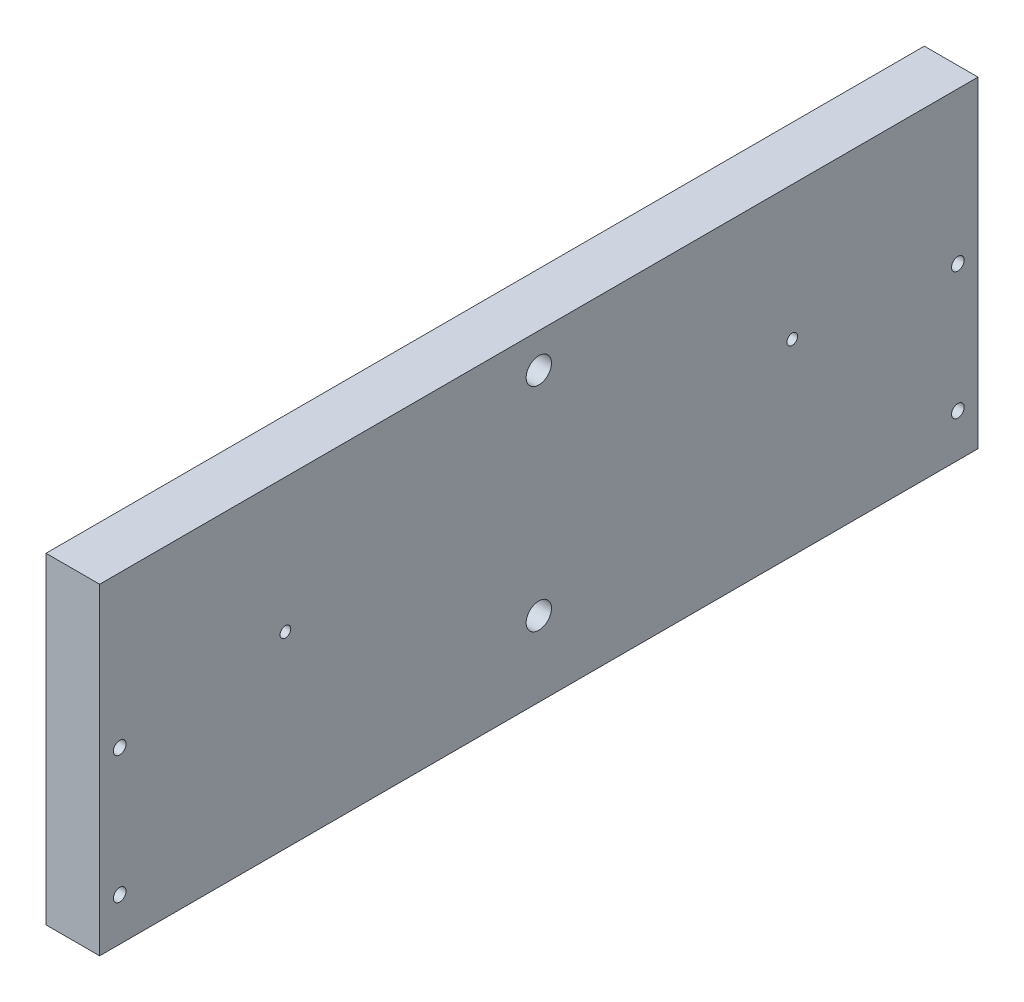
SolidWorks part; units mm, degrees
ref_plane "Front Plane" through (0, 0, 0) normal (0, 0, 1) x (1, 0, 0)
ref_plane "Top Plane" through (0, 0, 0) normal (0, 1, 0) x (1, 0, 0)
ref_plane "Right Plane" through (0, 0, 0) normal (1, 0, 0) x (0, 0, -1)
sketch "Sketch1" plane through (0, 0, 0) normal (1, 0, 0) x (0, 0, -1)
  line L1 (0, 0) -> (207.9625, 0)
  line L2 (0, 0) -> (0, 76.2)
  line L3 (0, 76.2) -> (207.9625, 76.2)
  line L4 (207.9625, 0) -> (207.9625, 76.2)
  line L5 (103.9812, 76.2) -> (103.9812, 0) construction
  line L6 (43.9813, 44.45) -> (163.9812, 44.45) construction
  line L7 (103.9813, 68.072) -> (103.9813, 17.78) construction
  circle A0 centre (103.9813, 68.072) radius 3
  circle A1 centre (103.9813, 17.78) radius 3
  circle A2 centre (43.9813, 44.45) radius 1.27
  circle A3 centre (163.9812, 44.45) radius 1.27
  circle A4 centre (4.7625, 40.3225) radius 1.5
  circle A5 centre (4.7625, 10.16) radius 1.5
  circle A6 centre (203.2, 40.3225) radius 1.5
  circle A7 centre (203.2, 10.16) radius 1.5
  point P17 (103.9813, 44.45)
  dimension "D3" = 6
  dimension "D4" = 6
  dimension "D5" = 2.54
  dimension "D6" = 2.54
  dimension "D9" = 3
  dimension "D1" = 76.2
  dimension "D2" = 207.9625
  dimension "D7" = 50.292
  dimension "D8" = 120
  dimension "D10" = 30.1625
  dimension "D11" = 10.16
  dimension "D12" = 4.7625
  dimension "D13" = 4.7625
  dimension "D14" = 17.78
  dimension "D15" = 44.45
extrude "Boss-Extrude1" add sketch "Sketch1" along normal blind 12.7
